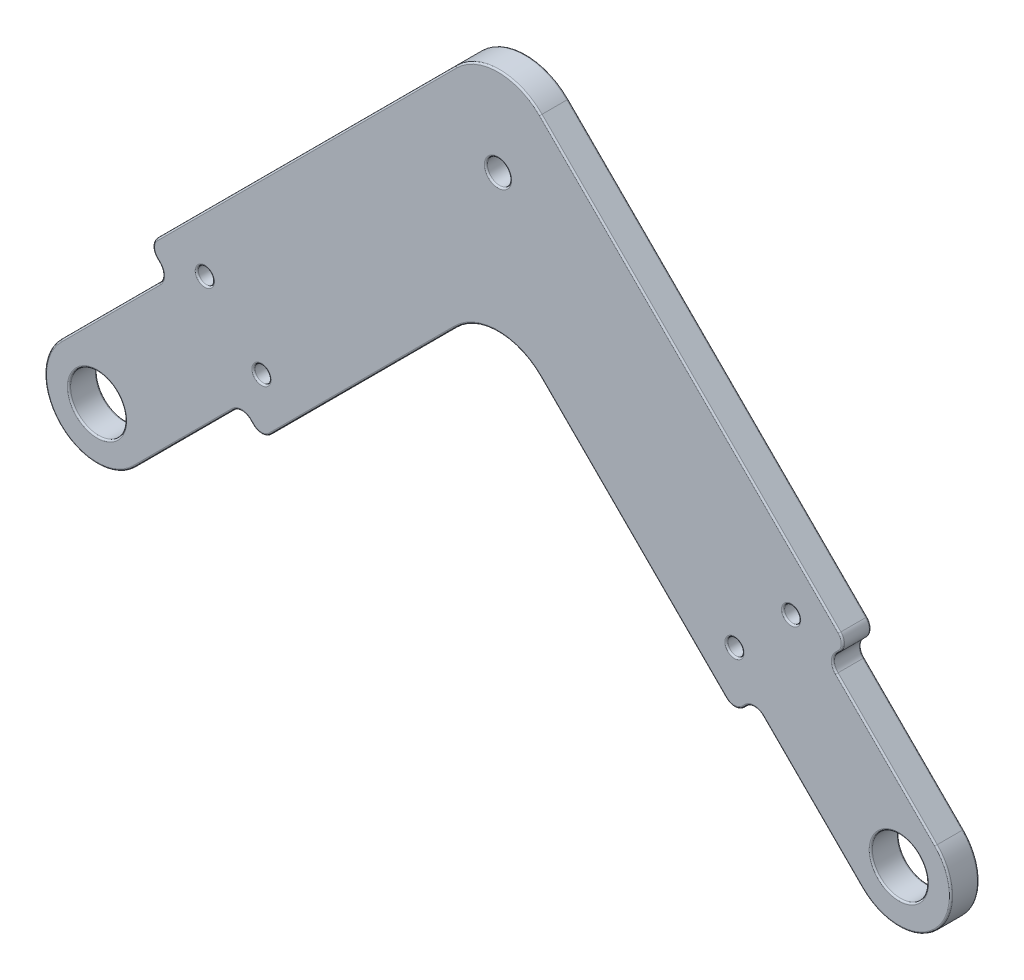
SolidWorks part; units mm, degrees
ref_plane "Front Plane" through (0, 0, 0) normal (0, 0, 1) x (1, 0, 0)
ref_plane "Top Plane" through (0, 0, 0) normal (0, 1, 0) x (1, 0, 0)
ref_plane "Right Plane" through (0, 0, 0) normal (1, 0, 0) x (0, 0, -1)
sketch "Sketch1" plane through (0, 0, 0) normal (0, 0, 1) x (1, 0, 0)
  line L0 (100, 0) -> (-100, 0)
  line L3 (-100, 0) -> (0, 100) construction
  line L4 (0, 100) -> (100, 0) construction
  line L5 (0, 0) -> (-50, 50) construction
  line L7 (0, 100) -> (0, 60) construction
  line L9 (-40, 60) -> (40, 60) construction
  circle A0 centre (-100, 0) radius 20
  circle A1 centre (0, 0) radius 20
  circle A2 centre (100, 0) radius 19.9987
  point P4 (0, 0)
  point P13 (0, 0)
  point P14 (0, 0)
  dimension "D5" = 40
  dimension "D6" = 39.9975
  dimension "D1" = 200
  dimension "D2" = 90
  dimension "D3" = 90
  dimension "D4" = 80
  dimension "D7" = 141.4214
  dimension "D8" = 70.7107
sketch "Sketch2" plane through (0, 0, 0) normal (0, 0, 1) x (1, 0, 0)
  line L0 (-56.5165, 43.4835) -> (-40, 60) construction
  line L1 (-100, 0) -> (0, 100) construction
  line L2 (-40, 60) -> (40, 60) construction
  line L3 (40, 60) -> (86.565, 13.435) construction
  line L4 (0, 100) -> (100, 0) construction
  line L5 (-49.4454, 36.4124) -> (-35.8579, 50)
  line L6 (-35.8579, 50) -> (35.8579, 50)
  line L7 (35.8579, 50) -> (79.4939, 6.364)
  line L8 (-63.5876, 50.5546) -> (-44.1421, 70)
  line L9 (-44.1421, 70) -> (44.1421, 70)
  line L10 (44.1421, 70) -> (93.636, 20.5061)
  line L11 (-63.5876, 50.5546) -> (-49.4454, 36.4124)
  line L12 (93.636, 20.5061) -> (79.4939, 6.364)
  line L13 (81.9688, 8.8388) -> (95.4038, -4.5962)
  line L14 (91.1612, 18.0312) -> (104.5962, 4.5962)
  line L15 (90.1005, 24.0416) -> (75.9584, 9.8995) construction
  line L16 (0, 100) -> (0, 60) construction
  line L17 (-6, 70) -> (-3.4486, 84.7178)
  line L18 (6, 70) -> (3.4486, 84.7178)
  circle A0 centre (100, 0) radius 3.5
  circle A1 centre (100, 0) radius 10 construction
  circle A3 centre (79.4939, 13.435) radius 1
  circle A4 centre (86.565, 20.5061) radius 1
  circle A5 centre (0, 60) radius 1.5
  circle A6 centre (0, 84.12) radius 1.5
  circle A8 centre (-50, 50) radius 1.5
  arc A9 (104.5962, 4.5962) -> (95.4038, -4.5962) centre (100, 0) cw
  arc A10 (-3.4486, 84.7178) -> (3.4486, 84.7178) centre (0, 84.12) cw
  point P51 (0, 70)
  dimension "D4" = 20
  dimension "D5" = 7
  dimension "D9" = 2
  dimension "D12" = 3
  dimension "D17" = 3
  dimension "D6" = 6.5
  dimension "D18" = 3
  dimension "D14" = 3.5
  dimension "D19" = 2
  dimension "D3" = 27.5
  dimension "D7" = 19
  dimension "D8" = 5
  dimension "D10" = 5
  dimension "D11" = 5
  dimension "D13" = 14.12
  dimension "D15" = 6
  dimension "D16" = 6
  dimension "D1" = 10
  dimension "D2" = 10
sketch "Sketch3" plane through (0, 0, 0) normal (0, 0, 1) x (1, 0, 0)
  line L0 (-86.565, 13.435) -> (-50, 50) construction
  line L1 (-100, 0) -> (0, 100) construction
  line L2 (-50, 50) -> (-13.435, 13.435) construction
  line L3 (0, 0) -> (-50, 50) construction
  line L4 (-79.4939, 6.364) -> (-50, 35.8579)
  line L5 (-50, 35.8579) -> (-20.5061, 6.364)
  line L6 (-93.636, 20.5061) -> (-50, 64.1421)
  line L7 (-50, 64.1421) -> (-6.364, 20.5061)
  line L10 (-91.1612, 18.0312) -> (-104.5962, 4.5962)
  line L11 (-81.9688, 8.8388) -> (-95.4038, -4.5962)
  line L12 (-18.0312, 8.8388) -> (-4.5962, -4.5962)
  line L13 (-8.8388, 18.0312) -> (4.5962, 4.5962)
  line L14 (-90.1005, 24.0416) -> (-75.9584, 9.8995) construction
  line L15 (-24.0416, 9.8995) -> (-9.8995, 24.0416) construction
  line L16 (-93.636, 20.5061) -> (-91.1612, 18.0312)
  line L17 (-79.4939, 6.364) -> (-81.9688, 8.8388)
  line L18 (-18.0312, 8.8388) -> (-20.5061, 6.364)
  line L19 (-6.364, 20.5061) -> (-8.8388, 18.0312)
  circle A0 centre (-100, 0) radius 10 construction
  circle A1 centre (-100, 0) radius 3.5
  circle A2 centre (0, 0) radius 10 construction
  circle A3 centre (0, 0) radius 3.5
  circle A6 centre (-86.565, 20.5061) radius 1
  circle A7 centre (-79.4939, 13.435) radius 1
  circle A8 centre (-13.435, 20.5061) radius 1
  circle A9 centre (-20.5061, 13.435) radius 1
  circle A10 centre (-50, 50) radius 1.5 construction
  circle A11 centre (-50, 50) radius 1.5
  arc A12 (4.5962, 4.5962) -> (-4.5962, -4.5962) centre (0, 0) cw
  arc A13 (-104.5962, 4.5962) -> (-95.4038, -4.5962) centre (-100, 0) ccw
  point P9 (0, 0)
  point P11 (0, 0)
  dimension "D1" = 20
  dimension "D2" = 7
  dimension "D9" = 2
  dimension "D13" = 2
  dimension "D3" = 6.5
  dimension "D16" = 3
  dimension "D17" = 3
  dimension "D18" = 6.5
  dimension "D6" = 19
  dimension "D7" = 3.5
  dimension "D8" = 19
  dimension "D10" = 5
  dimension "D11" = 5
  dimension "D12" = 3.5
  dimension "D14" = 5
  dimension "D15" = 5
  dimension "D19" = 5
  dimension "D20" = 5
  dimension "D4" = 10
  dimension "D5" = 10
sketch "Sketch4" plane through (0, 0, 0) normal (0, 0, 1) x (1, 0, 0)
  line L6 (-57.5, 92.6154) -> (57.5, 92.6154)
  line L7 (57.5, 92.6154) -> (57.5, 82.6154)
  line L8 (57.5, 82.6154) -> (44.1421, 70)
  line L9 (44.1421, 70) -> (-44.1421, 70)
  line L10 (-44.1421, 70) -> (-57.5, 82.6154)
  line L11 (-57.5, 82.6154) -> (-57.5, 92.6154)
  line L12 (-4, 60) -> (-4, 70)
  line L13 (4, 60) -> (4, 70)
  line L14 (-22.5, 84.1154) -> (22.5, 84.1154) construction
  line L15 (-22.5, 88.6154) -> (22.5, 88.6154)
  line L16 (-22.5, 79.6154) -> (22.5, 79.6154)
  arc A0 (-4, 60) -> (4, 60) centre (0, 60) ccw
  arc A1 (-22.5, 88.6154) -> (-22.5, 79.6154) centre (-22.5, 84.1154) ccw
  circle A2 centre (0, 60) radius 1.5 construction
  arc A4 (22.5, 79.6154) -> (22.5, 88.6154) centre (22.5, 84.1154) ccw
  point P2 (0, 92.6154)
  point P15 (0, 84.1154)
  dimension "D3" = 4
  dimension "D8" = 2.5
  dimension "D1" = 115
  dimension "D2" = 10
  dimension "D4" = 45
  dimension "D5" = 9
  dimension "D6" = 12.6154
  dimension "D7" = 4
extrude "Boss-Extrude1" add sketch "Sketch3" along normal blind 3.5
fillet "Fillet1" radius 7.5 2 edges at (-50, 35.8579, 1.75) (-50, 64.1421, 1.75)
fillet "Fillet2" radius 1.5 8 edges at (-91.1612, 18.0312, 1.75) (-93.636, 20.5061, 1.75) (-79.4939, 6.364, 1.75) (-81.9688, 8.8388, 1.75) (-20.5061, 6.364, 1.75) (-18.0312, 8.8388, 1.75) (-6.364, 20.5061, 1.75) (-8.8388, 18.0312, 1.75)
fillet "Fillet3" radius 0.2 62 edges at (-48.5, 50, 0) (-48.5, 50, 3.5) (-19.5061, 13.435, 0) (-19.5061, 13.435, 3.5) (-12.435, 20.5061, 0) (-12.435, 20.5061, 3.5) (-78.4939, 13.435, 0) (-78.4939, 13.435, 3.5) (-85.565, 20.5061, 0) (-85.565, 20.5061, 3.5) (3.5, 0, 0) (3.5, 0, 3.5) (-96.5, 0, 0) (-96.5, 0, 3.5) (-80.7313, 7.6014, 0) (-66.8683, 18.9896, 0) (-33.1317, 18.9896, 0) (-19.2687, 7.6014, 0) (-10.7834, 1.591, 0) (4.5962, -4.5962, 0) (-1.591, 10.7834, 0) (-7.6014, 19.2687, 0) (-26.0607, 40.2028, 0) (-92.3986, 19.2687, 0) (-98.409, 10.7834, 0) (-104.5962, -4.5962, 0) (-89.2166, 1.591, 0) (-80.7313, 7.6014, 3.5) (-66.8683, 18.9896, 3.5) (-33.1317, 18.9896, 3.5) (-19.2687, 7.6014, 3.5) (-10.7834, 1.591, 3.5) (4.5962, -4.5962, 3.5) (-1.591, 10.7834, 3.5) (-7.6014, 19.2687, 3.5) (-26.0607, 40.2028, 3.5) (-73.9393, 40.2028, 3.5) (-92.3986, 19.2687, 3.5) (-98.409, 10.7834, 3.5) (-104.5962, -4.5962, 3.5) (-89.2166, 1.591, 3.5) (-50, 61.0355, 0) (-50, 61.0355, 3.5) (-50, 32.7513, 0) (-50, 32.7513, 3.5) (-6.9853, 20.5061, 0) (-20.5061, 6.9853, 0) (-79.4939, 6.9853, 0) (-93.0147, 20.5061, 0) (-6.9853, 20.5061, 3.5) (-20.5061, 6.9853, 3.5) (-79.4939, 6.9853, 3.5) (-93.0147, 20.5061, 3.5) (-91.7825, 18.0312, 0) (-91.7825, 18.0312, 3.5) (-81.9688, 8.2175, 0) (-81.9688, 8.2175, 3.5) (-18.0312, 8.2175, 0) (-18.0312, 8.2175, 3.5) (-8.2175, 18.0312, 0) (-8.2175, 18.0312, 3.5) (-73.9393, 40.2028, 0)
